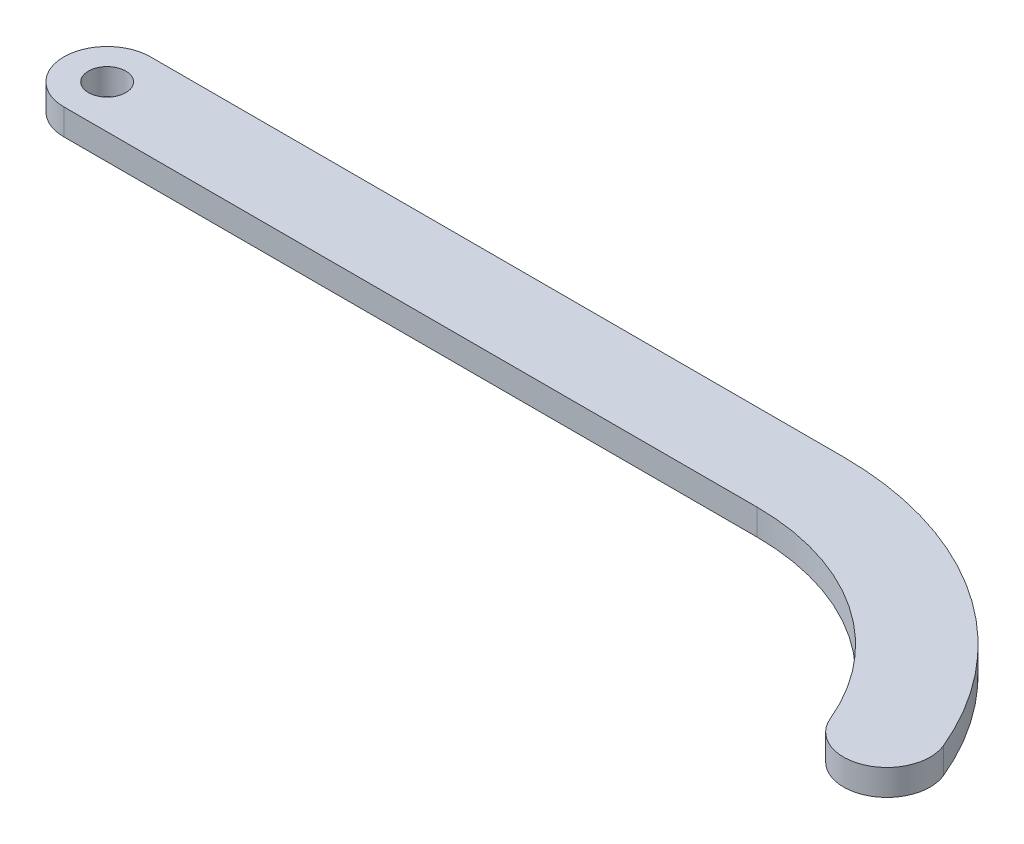
SolidWorks part; units mm, degrees
material "Acrylic (Medium-high impact)"
ref_plane "Front Plane" through (0, 0, 0) normal (0, 0, 1) x (1, 0, 0)
ref_plane "Top Plane" through (0, 0, 0) normal (0, 1, 0) x (1, 0, 0)
ref_plane "Right Plane" through (0, 0, 0) normal (1, 0, 0) x (0, 0, -1)
sketch "Sketch1" plane through (0, 0, 0) normal (0, 1, 0) x (1, 0, 0)
  line L0 (0, 0) -> (80, 0) construction
  line L1 (0, 5) -> (80, 5)
  line L2 (80, -5) -> (0, -5)
  line L3 (114.6154, -18.0769) -> (105.3846, -21.9231) construction
  arc A0 (80, 0) -> (110, -20) centre (80, -32.5) cw construction
  arc A1 (80, 5) -> (114.6154, -18.0769) centre (80, -32.5) cw
  arc A2 (114.6154, -18.0769) -> (105.3846, -21.9231) centre (110, -20) cw
  arc A3 (105.3846, -21.9231) -> (80, -5) centre (80, -32.5) ccw
  arc A4 (0, -5) -> (0, 5) centre (0, 0) cw
  dimension "D1" = 80
  dimension "D4" = 5
  dimension "D2" = 30
  dimension "D3" = 20
extrude "Boss-Extrude1" add sketch "Sketch1" along normal blind 3
sketch "Sketch2" plane through (0, 3, 0) normal (0, 1, 0) x (1, 0, 0)
  circle A0 centre (0, 0) radius 2.159
  dimension "D1" = 4.318
extrude "Cut-Extrude1" cut sketch "Sketch2" against normal up to next
